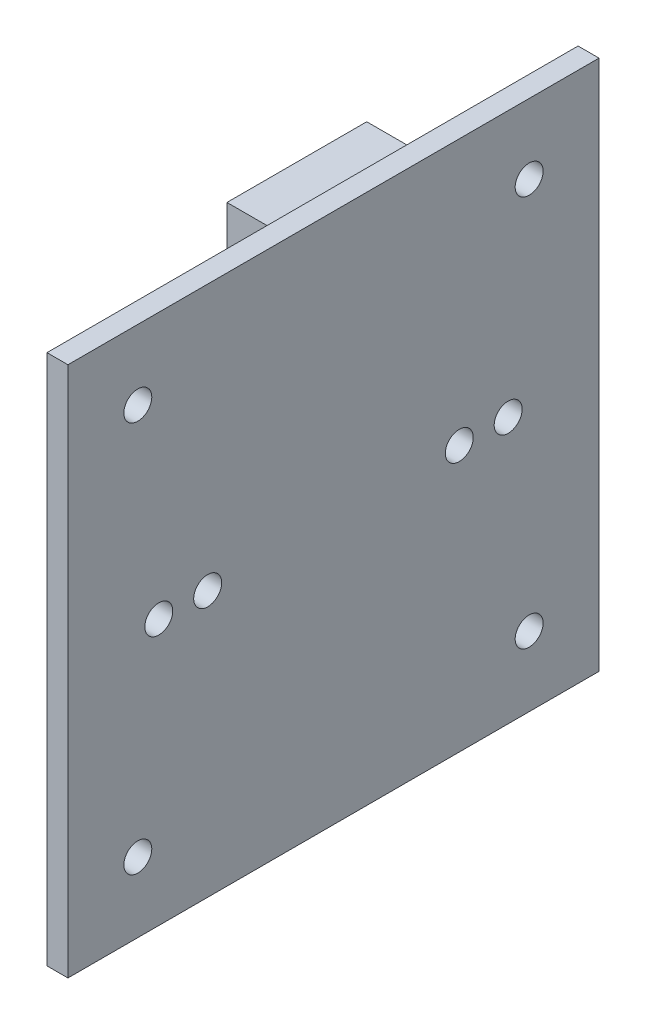
SolidWorks part; units mm, degrees
ref_plane "前视基准面" through (0, 0, 0) normal (0, 0, 1) x (1, 0, 0)
ref_plane "上视基准面" through (0, 0, 0) normal (0, 1, 0) x (1, 0, 0)
ref_plane "右视基准面" through (0, 0, 0) normal (1, 0, 0) x (0, 0, -1)
sketch "草图1" plane through (0, 0, 0) normal (1, 0, 0) x (0, 0, -1)
  line L1 (-19, 19) -> (19, 19)
  line L2 (-19, 19) -> (-19, -19)
  line L3 (-19, -19) -> (19, -19)
  line L4 (19, 19) -> (19, -19)
  line L5 (-19, 19) -> (19, -19) construction
  line L6 (-19, -19) -> (19, 19) construction
  point P0 (0, 0)
extrude "凸台-拉伸1" add sketch "草图1" along normal blind 1.5 contours L2 L1 L4 L3
sketch "草图2" plane through (1.5, 0, 0) normal (1, 0, 0) x (0, 0, -1)
  circle A0 centre (-14, 14) radius 1
  circle A1 centre (-14, -14) radius 1
  circle A2 centre (14, -14) radius 1
  circle A3 centre (14, 14) radius 1
  circle A4 centre (-12.5, 0) radius 1
  circle A5 centre (12.5, 0) radius 1
  point P0 (0, 0)
extrude "切除-拉伸1" cut sketch "草图2" against normal blind 1.5
sketch "草图3" plane through (0, 0, 0) normal (-1, 0, 0) x (0, 0, 1)
  line L1 (-10.8787, 14.8676) -> (-0.8787, 14.8676)
  line L2 (-10.8787, 14.8676) -> (-10.8787, 10.8676)
  line L3 (-10.8787, 10.8676) -> (-0.8787, 10.8676)
  line L4 (-0.8787, 14.8676) -> (-0.8787, 10.8676)
extrude "凸台-拉伸2" add sketch "草图3" along normal blind 7 contours L2 L1 L4 L3
sketch "草图4" plane through (-7, 0, 0) normal (-1, 0, 0) x (0, 0, 1)
  line L7 (-10.6287, 14.6176) -> (-1.1287, 14.6176)
  line L8 (-10.6287, 14.6176) -> (-10.6287, 11.1176)
  line L9 (-10.6287, 11.1176) -> (-1.1287, 11.1176)
  line L10 (-1.1287, 14.6176) -> (-1.1287, 11.1176)
  point P12 (-5.8787, 12.8676)
extrude "切除-拉伸4" cut sketch "草图4" against normal blind 5 contours L8 L7 L10 L9
sketch "草图6" plane through (1.5, 0, 0) normal (1, 0, 0) x (0, 0, -1)
  circle A0 centre (-9, 0) radius 1
  circle A1 centre (9, 0) radius 1
extrude "切除-拉伸6" cut sketch "草图6" against normal blind 10
